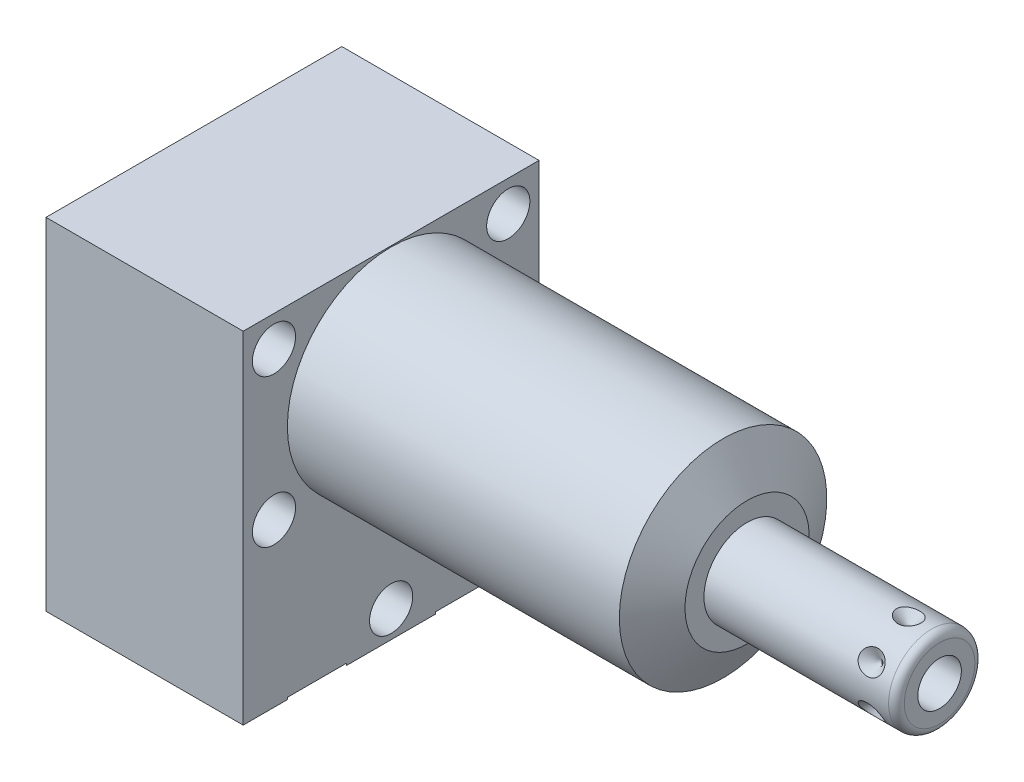
SolidWorks part; units mm, degrees
material "Alloy Steel"
ref_plane "Front Plane" through (0, 0, 0) normal (0, 0, 1) x (1, 0, 0)
ref_plane "Top Plane" through (0, 0, 0) normal (0, 1, 0) x (1, 0, 0)
ref_plane "Right Plane" through (0, 0, 0) normal (1, 0, 0) x (0, 0, -1)
ref_plane "Plane1" through (0, 0, 0) normal (1, 0, 0) x (0, 0, -1)
sketch "Sketch1" plane through (0, 0, 0) normal (1, 0, 0) x (0, 0, -1)
  line L0 (-19.05, 13.4874) -> (-19.05, -30.4546)
  line L1 (-19.05, -30.4546) -> (19.05, -30.4546)
  line L2 (19.05, -30.4546) -> (19.05, 13.4874)
  line L3 (19.05, 13.4874) -> (-19.05, 13.4874)
  line L4 (0, -32.6517) -> (0, 15.6845) construction
  dimension "D1" = 38.1
  dimension "D2" = 43.942
  dimension "D3" = 13.4874
extrude "Extrude1" add sketch "Sketch1" along normal blind 45.847 and the other way blind 25.4
ref_plane "Plane2" through (0, 0, 0) normal (1, 0, 0) x (0, 0, -1)
sketch "Sketch2" plane through (0, 0, 0) normal (1, 0, 0) x (0, 0, -1)
  line L0 (-14.6964, 0) -> (14.6964, 0) construction
  line L5 (19.05, 13.4874) -> (-19.05, 13.4874)
  line L6 (-19.05, 13.4874) -> (-19.05, -30.4546)
  line L7 (-19.05, -30.4546) -> (19.05, -30.4546)
  line L8 (19.05, -30.4546) -> (19.05, 13.4874)
  line L9 (19.05, 13.4874) -> (-19.05, 13.4874)
  line L10 (-19.05, 13.4874) -> (-19.05, -30.4546)
  line L11 (-19.05, -30.4546) -> (19.05, -30.4546)
  line L12 (19.05, -30.4546) -> (19.05, 13.4874)
  circle A0 centre (0, 0) radius 13.3604
  dimension "D1" = 26.7208
  dimension "D2" = 0
extrude "Cut-Extrude1" cut sketch "Sketch2" along normal up to next
ref_plane "Plane3" through (0, 0, 0) normal (0, 0, 1) x (1, 0, 0)
sketch "Sketch3" plane through (0, 0, 0) normal (0, 0, 1) x (1, 0, 0)
  line L0 (42.7527, 13.3604) -> (45.847, 8.001)
  line L1 (42.598, 0) -> (46.0017, 0) construction
  line L2 (45.847, 13.3604) -> (45.847, 8.001)
  line L3 (45.847, 13.3604) -> (42.7527, 13.3604)
  line L4 (45.847, 13.3604) -> (0, 13.3604) construction
  line L5 (45.847, -13.3604) -> (45.847, 13.3604) construction
  dimension "D1" = 30
  dimension "D2" = 16.002
revolve "Cut-Revolve1" cut sketch "Sketch3" angle 360 about L1
ref_plane "Plane4" through (-22.733, -19.8374, 9.525) normal (0, 0, 1) x (0, 1, 0)
sketch "S2D0002" plane through (-22.733, -19.8374, 9.525) normal (0, 0, 1) x (0, 1, 0)
  line L0 (-0.8128, 0) -> (3.7338, 0)
  line L1 (3.7338, 0) -> (3.2938, -2.0701)
  line L2 (3.2938, -2.0701) -> (2.6416, -2.7223)
  line L3 (2.6416, -2.7223) -> (2.6416, -13.97)
  line L4 (2.6416, -13.97) -> (-0.8128, -13.97)
  line L5 (-0.8128, -13.97) -> (-0.8128, 0)
  line L6 (-0.8128, -14.6685) -> (-0.8128, 0.6985) construction
  line L7 (19.8374, -65.4857) -> (19.8374, -22.733) construction
  dimension "D1" = 13.97
  dimension "D2" = 20.6502
revolve "Cut-Revolve2" cut sketch "S2D0002" angle 360 about L6
ref_plane "Plane5" through (-22.733, -19.8374, -9.525) normal (0, 0, 1) x (0, 1, 0)
sketch "Sketch5" plane through (-22.733, -19.8374, -9.525) normal (0, 0, 1) x (0, 1, 0)
  line L0 (-0.8128, 0) -> (3.7338, 0)
  line L1 (3.7338, 0) -> (3.2938, -2.0701)
  line L2 (3.2938, -2.0701) -> (2.6416, -2.7223)
  line L3 (2.6416, -2.7223) -> (2.6416, -13.97)
  line L4 (2.6416, -13.97) -> (-0.8128, -13.97)
  line L5 (-0.8128, -13.97) -> (-0.8128, 0)
  line L6 (-0.8128, -14.6685) -> (-0.8128, 0.6985) construction
  line L7 (19.8374, -65.4857) -> (19.8374, -22.733) construction
  dimension "D1" = 13.97
  dimension "D2" = 20.6502
revolve "Cut-Revolve3" cut sketch "Sketch5" angle 360 about L6
ref_plane "Plane6" through (-8.7376, -30.2006, 9.525) normal (0, 0, 1) x (-1, 0, 0)
sketch "Sketch14" plane through (-25.4, 0, 0) normal (-1, 0, 0) x (0, 0, 1)
  circle A0 centre (-9.525, -20.6502) radius 7.9375
  circle A1 centre (9.525, -20.6502) radius 7.9375
  dimension "D1" = 15.875
extrude "Cut-Extrude2" cut sketch "Sketch14" against normal blind 2.667
sketch "Sketch6" plane through (-8.7376, -30.2006, 9.525) normal (0, 0, 1) x (-1, 0, 0)
  line L0 (16.6624, -43.688) -> (16.6624, 0.254) construction
  line L1 (6.1836, 0) -> (5.641, -2.5527)
  line L2 (5.641, -2.5527) -> (4.9771, -3.2166)
  line L3 (4.9771, -3.2166) -> (4.9771, -17.272)
  line L4 (4.9771, -17.272) -> (0, -17.272)
  line L5 (0, -17.272) -> (0, 0)
  line L6 (0, -18.1356) -> (0, 0.8636) construction
  line L7 (6.1836, 0) -> (9.5237, 0)
  line L8 (9.5237, 0) -> (9.5237, 0.254)
  line L9 (16.6624, 0.254) -> (-8.7376, 0.254) construction
  line L10 (9.5237, 0.254) -> (0, 0.254)
  line L11 (0, 0.254) -> (0, 0)
  dimension "D1" = 19.0475
  dimension "D2" = 0.254
  dimension "D3" = 16.6624
revolve "Cut-Revolve4" cut sketch "Sketch6" angle 360 about L6
ref_plane "Plane7" through (-8.7376, -30.2006, -9.525) normal (0, 0, 1) x (-1, 0, 0)
sketch "Sketch7" plane through (-8.7376, -30.2006, -9.525) normal (0, 0, 1) x (-1, 0, 0)
  line L0 (16.6624, -43.688) -> (16.6624, 0.254) construction
  line L1 (6.1849, 0) -> (5.6423, -2.5527)
  line L2 (5.6423, -2.5527) -> (4.9784, -3.2166)
  line L3 (4.9784, -3.2166) -> (4.9784, -17.272)
  line L4 (4.9784, -17.272) -> (0, -17.272)
  line L5 (0, -17.272) -> (0, 0)
  line L6 (0, -18.1356) -> (0, 0.8636) construction
  line L7 (6.1849, 0) -> (9.5237, 0)
  line L8 (9.5237, 0) -> (-8.7376, 0) construction
  line L9 (9.5237, 0) -> (9.5237, 0.254)
  line L10 (16.6624, 0.254) -> (-8.7376, 0.254) construction
  line L11 (9.5237, 0.254) -> (0, 0.254)
  line L12 (0, 0.254) -> (0, 0)
  dimension "D1" = 16.6624
  dimension "D2" = 9.9568
  dimension "D3" = 19.0475
revolve "Cut-Revolve5" cut sketch "Sketch7" angle 360 about L6
ref_plane "Plane8" through (0, 0, 0) normal (0, 0, 1) x (1, 0, 0)
sketch "Sketch8" plane through (0, 0, 0) normal (0, 0, 1) x (1, 0, 0)
  line L0 (45.847, 0) -> (45.847, 5.5562)
  line L1 (45.847, 5.5562) -> (69.6214, 5.5562)
  line L2 (70.6374, 4.5403) -> (70.6374, 0)
  line L3 (70.6374, 0) -> (45.847, 0)
  line L4 (44.8323, 0) -> (67.1563, 0) construction
  line L5 (45.847, -8.001) -> (45.847, 8.001) construction
  line L6 (-25.4, 13.4874) -> (-25.4, -30.4546) construction
  arc A0 (70.6374, 4.5403) -> (69.6214, 5.5562) centre (69.6214, 4.5403) ccw
  point P0 (45.847, 0)
  dimension "D3" = 1.016
  dimension "D1" = 96.0374
  dimension "D2" = 11.1125
revolve "Revolve1" add sketch "Sketch8" angle 360 about L4
ref_plane "Plane9" through (66.1416, -2.8067, 0) normal (0, 0, 1) x (0, -1, 0)
sketch "S2D0001" plane through (66.1416, -2.8067, 0) normal (0, 0, 1) x (0, -1, 0)
  line L0 (0, 4.4958) -> (0, -5.6642)
  line L1 (0, -5.6642) -> (-2.8067, -7.3506)
  line L2 (0, 4.4958) -> (-2.8067, 4.4958)
  line L3 (-2.8067, 4.4958) -> (-2.8067, -7.3506)
  line L4 (-2.8067, -12.4388) -> (-2.8067, 0.5923) construction
  line L5 (1.7335, 4.4958) -> (-7.3469, 4.4958) construction
  dimension "D1" = 5.6134
  dimension "D2" = 10.16
  dimension "D3" = 59
revolve "Cut-Revolve6" cut sketch "S2D0001" angle 360 about L4
ref_plane "Plane10" through (-25.4, -30.2006, 0) normal (0, -1, 0) x (0, 0, -1)
sketch "Sketch10" plane through (-25.4, -30.2006, 0) normal (0, -1, 0) x (0, 0, -1)
  circle A0 centre (-9.525, 16.6624) radius 6.4389
  circle A1 centre (-9.525, 16.6624) radius 6.1836 construction
  dimension "D1" = 12.8778
extrude "Extrude2" add sketch "Sketch10" along normal blind 1.651
sketch "Sketch11" plane through (-22.733, 0, 0) normal (-1, 0, 0) x (0, 0, 1)
  circle A0 centre (9.525, -20.6502) radius 4.8006
  circle A1 centre (9.525, -20.6502) radius 4.5466 construction
  dimension "D1" = 9.6012
ref_plane "Plane11" through (-25.4, 0, 0) normal (1, 0, 0) x (0, 0, -1)
extrude "Extrude3" add sketch "Sketch11" along normal up to surface (2.667 mm away) up to plane "Plane11"
ref_plane "Plane12" through (62.1792, -5.5562, 0) normal (0, 0, 1) x (-1, 0, 0)
sketch "Sketch12" plane through (62.1792, -5.5562, 0) normal (0, 0, 1) x (-1, 0, 0)
  line L0 (-4.4958, 0) -> (-2.9083, 0)
  line L1 (-2.9083, 0) -> (-4.4958, -1.5875)
  line L2 (-4.4958, 0) -> (-4.4958, -1.5875)
  line L3 (-4.4958, -3.434) -> (-4.4958, 0.0794) construction
  line L4 (16.3322, 0) -> (-7.4422, 0) construction
  line L5 (-8.4582, -1.016) -> (-8.4582, -10.0965) construction
  dimension "D1" = 3.9624
  dimension "D2" = 45
  dimension "D3" = 3.175
revolve "Cut-Revolve7" cut sketch "Sketch12" angle 360 about L3
pattern_circular "CirPattern1" count 6 over 360 about axis through (45.848, 0, 0) along (-1, 0, 0) of "Cut-Revolve7"
hole_wizard "Hole1" positions "Sketch17" profile "Sketch16" legacy end condition up to next
sketch "Sketch17" plane through (0, 0, 0) normal (1, 0, 0) x (0, 0, -1)
  line L0 (0, 0) -> (0, 17.9298) construction
  line L1 (0, 0) -> (-24.6425, 0) construction
  point P0 (-15.0876, 9.525)
  point P10 (-15.0876, -9.525)
  point P12 (15.0876, 9.525)
  point P13 (15.0876, -9.525)
  point P14 (0, -26.9748)
  dimension "D1" = 9.525
  dimension "D2" = 15.0876
  dimension "D3" = 26.9748
sketch "Sketch16" plane through (0, 9.525, 15.0876) normal (0, 1, 0) x (0, 0, -1)
  line L0 (0, 0) -> (0, 25.4)
  line L1 (0, 25.4) -> (2.7813, 25.4)
  line L2 (2.7813, 25.4) -> (2.7813, 0)
  line L3 (2.7813, 0) -> (0, 0)
  line L4 (0, 110) -> (0, -10) construction
  dimension "Diameter" = 5.5626
  dimension "Depth" = 25.4
